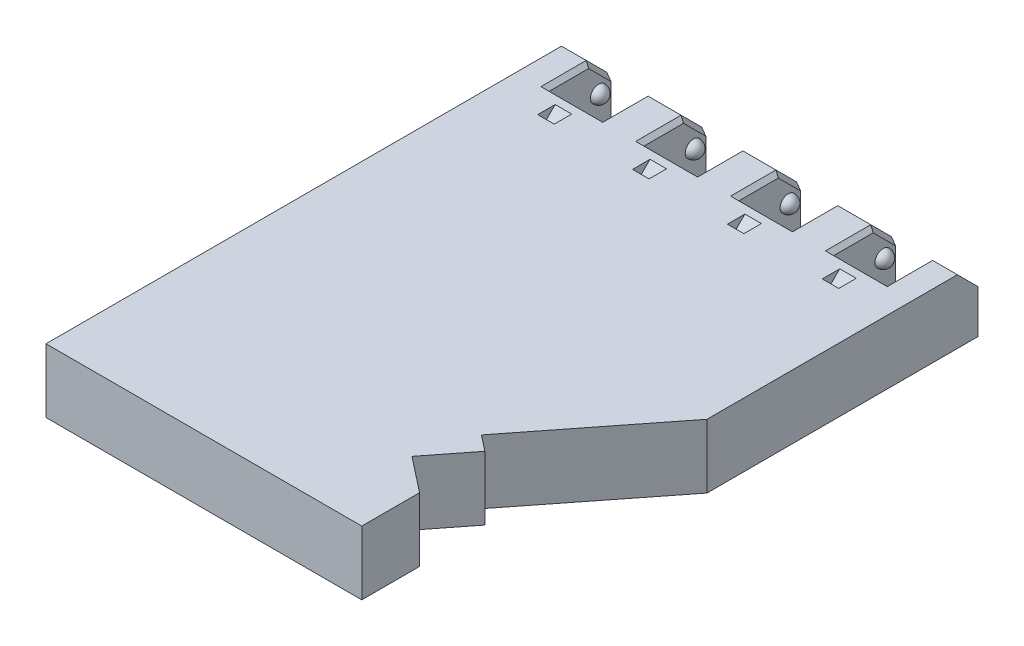
SolidWorks part; units mm, degrees
ref_plane "Front Plane" through (0, 0, 0) normal (0, 0, 1) x (1, 0, 0)
ref_plane "Top Plane" through (0, 0, 0) normal (0, 1, 0) x (1, 0, 0)
ref_plane "Right Plane" through (0, 0, 0) normal (1, 0, 0) x (0, 0, -1)
sketch "Sketch1" plane through (0, 0, 0) normal (0, 1, 0) x (1, 0, 0)
  line L0 (-106.7734, 72.7684) -> (-99.7734, 72.7684)
  line L1 (-99.7734, 72.7684) -> (-99.7734, 56.7684)
  line L2 (-99.7734, 56.7684) -> (-86.7734, 56.7684)
  line L3 (-86.7734, 56.7684) -> (-86.7734, 72.7684)
  line L4 (-86.7734, 72.7684) -> (-76.7734, 72.7684)
  line L5 (-76.7734, 72.7684) -> (-76.7734, 56.7684)
  line L6 (-76.7734, 56.7684) -> (-63.7734, 56.7684)
  line L7 (-63.7734, 56.7684) -> (-63.7734, 72.7684)
  line L8 (-63.7734, 72.7684) -> (-53.7734, 72.7684)
  line L9 (-53.7734, 72.7684) -> (-53.7734, 56.7684)
  line L10 (-53.7734, 56.7684) -> (-40.7734, 56.7684)
  line L11 (-40.7734, 56.7684) -> (-40.7734, 72.7684)
  line L12 (-40.7734, 72.7684) -> (-30.7734, 72.7684)
  line L13 (-30.7734, 72.7684) -> (-30.7734, 56.7684)
  line L14 (-30.7734, 56.7684) -> (-17.7734, 56.7684)
  line L15 (-17.7734, 56.7684) -> (-17.7734, 72.7684)
  line L16 (-17.7734, 72.7684) -> (-10.7734, 72.7684)
  line L17 (-106.7734, 72.7684) -> (-106.7734, -57.2316)
  line L19 (-10.7734, 7.0543) -> (-10.7734, 72.7684)
  line L36 (-106.7734, -57.2316) -> (-30.2052, -57.2316)
  line L39 (-34.8357, -23.5818) -> (-10.7734, 7.0543)
  line L47 (-30.2052, -43.2151) -> (-38.7537, -36.5009)
  line L48 (-38.7537, -36.5009) -> (-30.9832, -26.6077)
  line L49 (-30.9832, -26.6077) -> (-34.8357, -23.5818)
  line L51 (-30.2052, -43.2151) -> (-30.2052, -57.2316)
  dimension "D1" = 7
  dimension "D2" = 13
  dimension "D3" = 10
  dimension "D4" = 16
  dimension "D5" = 130
  dimension "D6" = 76.5682
  dimension "D7" = 65.7141
  dimension "D8" = 10.87
  dimension "D9" = 12.58
  dimension "D10" = 4.8987
  dimension "D11" = 38.956
extrude "Boss-Extrude1" add sketch "Sketch1" along normal blind 15.5 contours L19 L16 L15 L14 L13 L12 L11 L10 L9 L8 L7 L6 L5 L4 L3 L2 L1 L0 L17 L36 L51 L47 L48 L49 L39
ref_plane "Plane1" through (-99.7734, 0, 0) normal (1, 0, 0) x (0, 0, -1)
sketch "Sketch4" plane through (-99.7734, 0, 0) normal (1, 0, 0) x (0, 0, -1)
  line L0 (67.7684, 8) -> (71.7684, 8)
  line L1 (72.7684, 15.5) -> (72.7684, 0) construction
  line L2 (7.0543, 15.5) -> (72.7684, 15.5) construction
  arc A0 (71.7684, 8) -> (67.7684, 8) centre (69.7684, 8) ccw
  dimension "D2" = 2
  dimension "D1" = 3
  dimension "D3" = 4
  dimension "D4" = 7.5
revolve "Revolve1" add sketch "Sketch4" angle 360 about L0
ref_plane "Plane2" through (-93.2734, 0, 0) normal (1, 0, 0) x (0, 0, -1)
mirror "Mirror1" about plane through (-93.2734, 0, 0) normal (1, 0, 0) of "Revolve1"
ref_plane "Plane3" through (-81.7734, 0, 0) normal (1, 0, 0) x (0, 0, -1)
mirror "Mirror2" about plane through (-81.7734, 0, 0) normal (1, 0, 0) of "Mirror1", "Revolve1"
ref_plane "Plane4" through (-58.7734, 0, 0) normal (1, 0, 0) x (0, 0, -1)
mirror "Mirror3" about plane through (-58.7734, 0, 0) normal (1, 0, 0) of "Mirror2", "Mirror1", "Revolve1"
ref_plane "Plane6" through (0, 0, -35) normal (0, 0, 1) x (1, 0, 0)
ref_plane "Plane7" through (0, -17.5, -17.5) normal (0, -0.7071, -0.7071) x (-1, 0, 0)
sketch "Sketch10" plane through (0, -17.5, -17.5) normal (0, -0.7071, -0.7071) x (-1, 0, 0)
  line L0 (22.2734, 55.1414) -> (26.2734, 55.1414)
  line L1 (26.2734, 55.1414) -> (26.2734, 25.1414)
  line L7 (22.2734, 25.1414) -> (26.2734, 25.1414)
  line L8 (22.2734, 25.1414) -> (22.2734, 55.1414)
  line L9 (10.7734, 4.9881) -> (10.7734, 51.4551) construction
  line L11 (30.7734, 40.1414) -> (17.7734, 40.1414) construction
  dimension "D1" = 30
  dimension "D2" = 4
  dimension "D3" = 11.5
  dimension "D4" = 15
extrude "Cut-Extrude1" cut sketch "Sketch10" along normal blind 3 contours L8 L0 L1 L7
ref_plane "Plane8" through (-35.7734, 0, 0) normal (1, 0, 0) x (0, 0, -1)
mirror "Mirror4" about plane through (-35.7734, 0, 0) normal (1, 0, 0) of "Cut-Extrude1"
ref_plane "Plane9" through (-58.7734, 0, 0) normal (1, 0, 0) x (0, 0, -1)
mirror "Mirror5" about plane through (-58.7734, 0, 0) normal (1, 0, 0) of "Mirror4", "Cut-Extrude1"
sketch "Sketch14" plane through (0, 0, 0) normal (0, -1, 0) x (-1, 0, 0)
  line L1 (25.6033, 49.2426) -> (25.6033, 53.2426)
  line L2 (25.6033, 53.2426) -> (22.8516, 53.2426)
  line L3 (22.8516, 53.2426) -> (22.8516, 49.2426)
  line L4 (22.8516, 49.2426) -> (25.6033, 49.2426)
  line L5 (26.2734, 39.2426) -> (22.2734, 39.2426) construction
  line L6 (10.7734, 7.0543) -> (10.7734, 72.7684) construction
  dimension "D1" = 2.7517
  dimension "D2" = 4
  dimension "D3" = 10
  dimension "D4" = 12.0782
extrude "Boss-Extrude2" add sketch "Sketch14" along normal blind 4
sketch "Sketch15" plane through (0, -4, 0) normal (0, -1, 0) x (1, 0, 0)
  line L0 (-26.4764, -47.7426) -> (-26.4764, -54.7426)
  line L1 (-26.4764, -54.7426) -> (-21.9785, -54.7426)
  line L2 (-21.9785, -54.7426) -> (-21.9785, -47.7426)
  line L3 (-26.4764, -47.7426) -> (-21.9785, -47.7426)
  line L4 (-25.6033, -53.2426) -> (-22.8516, -53.2426) construction
  line L8 (-22.8516, -49.2426) -> (-25.6033, -49.2426) construction
  line L9 (-10.7734, -7.0543) -> (-10.7734, -72.7684) construction
  point P6 (-24.2275, -53.2426)
  point P7 (-24.2275, -54.7426)
  dimension "D1" = 1.5
  dimension "D2" = 1.5
  dimension "D3" = 11.2051
extrude "Boss-Extrude3" add sketch "Sketch15" along normal blind 1
mirror "Mirror6" about plane through (-35.7734, 0, 0) normal (1, 0, 0) of "Boss-Extrude2", "Boss-Extrude3"
mirror "Mirror7" about plane through (-58.7734, 0, 0) normal (1, 0, 0) of "Mirror6", "Boss-Extrude2", "Boss-Extrude3"
chamfer "Chamfer9" distance 5 angle 45 1 edges at (-103.2734, 15.5, -72.7684)
chamfer "Chamfer10" distance 1 angle 45 2 edges at (-99.7734, 13, -70.2684) (-99.7734, 15.5, -62.2684)
chamfer "Chamfer15" distance 5 angle 45 1 edges at (-81.7734, 15.5, -72.7684)
chamfer "Chamfer16" distance 1 angle 45 2 edges at (-86.7734, 15.5, -62.2684) (-86.7734, 13, -70.2684)
chamfer "Chamfer17" distance 1 angle 45 2 edges at (-76.7734, 15.5, -62.2684) (-76.7734, 13, -70.2684)
chamfer "Chamfer18" distance 5 angle 45 3 edges at (-14.2734, 15.5, -72.7684) (-35.7734, 15.5, -72.7684) (-58.7734, 15.5, -72.7684)
chamfer "Chamfer19" distance 1 angle 45 10 edges at (-17.7734, 13, -70.2684) (-17.7734, 15.5, -62.2684) (-30.7734, 15.5, -62.2684) (-30.7734, 13, -70.2684) (-40.7734, 15.5, -62.2684) (-40.7734, 13, -70.2684) (-53.7734, 15.5, -62.2684) (-53.7734, 13, -70.2684) (-63.7734, 15.5, -62.2684) (-63.7734, 13, -70.2684)
